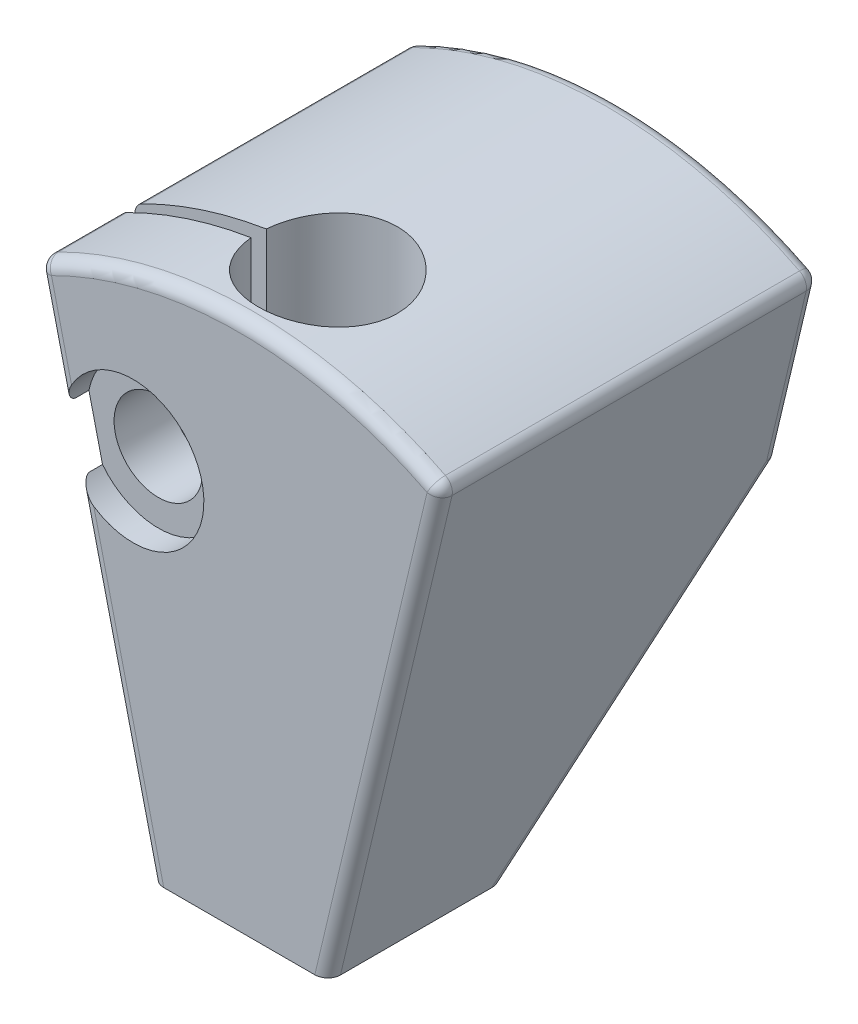
SolidWorks part; units mm, degrees
ref_plane "Plan de face" through (0, 0, 0) normal (0, 0, 1) x (1, 0, 0)
ref_plane "Plan de dessus" through (0, 0, 0) normal (0, 1, 0) x (1, 0, 0)
ref_plane "Plan de droite" through (0, 0, 0) normal (1, 0, 0) x (0, 0, -1)
sketch "Esquisse1" plane through (0, 0, 0) normal (1, 0, 0) x (0, 0, -1)
  line L0 (0, 33.3179) -> (0, -35.6026) construction
  line L1 (3.5, 0) -> (-3.5, 0)
  line L2 (-3.5, 0) -> (-3.5, 21)
  line L3 (-3.5, 21) -> (11.5, 21)
  line L4 (11.5, 21) -> (11.5, 12)
  line L5 (11.5, 12) -> (3.5, 0)
  dimension "D1" = 21
  dimension "D2" = 3.5
  dimension "D3" = 11.5
  dimension "D4" = 12
extrude "Extrusion1" add sketch "Esquisse1" along normal mid plane 16
sketch "Esquisse2" plane through (0, 0, 0) normal (0, 0, 1) x (1, 0, 0)
  line L0 (0, 0) -> (0, 21.9609) construction
  line L1 (-3.5, 0) -> (-8, 19)
  line L2 (8, 0) -> (-8, 0) construction
  line L3 (8, 21) -> (-8, 21) construction
  line L4 (-8, 21) -> (-8, 0) construction
  line L5 (3.5, 0) -> (8, 19)
  line L6 (-3.5, 0) -> (3.5, 0)
  arc A0 (8, 19) -> (-8, 19) centre (0, 4) ccw
  dimension "D1" = 2
  dimension "D2" = 7
extrude "Enlèv. mat.-Extru.1" cut sketch "Esquisse2" against normal through all and the other way through all flip side to cut
fillet "Congé1" radius 0.5 11 edges at (0, 12, -11.5) (5.75, 9.5, 3.5) (7.1711, 15.5, -11.5) (-7.1711, 15.5, -11.5) (0, 21, -11.5) (-8, 19, -4) (-5.75, 9.5, 3.5) (8, 19, -4) (0, 21, 3.5) (-4.9211, 6, -7.5) (4.9211, 6, -7.5)
sketch "Esquisse3" plane through (0, 0, 0) normal (0, 1, 0) x (1, 0, 0)
  circle A0 centre (0, 0) radius 2.75
  dimension "D1" = 5.5
extrude "Enlèv. mat.-Extru.3" cut sketch "Esquisse3" along normal through all
sketch "Esquisse4" plane through (0, 0, 0) normal (0, 1, 0) x (1, 0, 0)
  line L0 (0, 0) -> (-9.5091, 0) construction
  line L1 (-7.9236, 11) -> (-7.9236, -3) construction
  line L2 (-7.9236, 0.3) -> (0, 0.3)
  line L3 (-7.9236, 0.3) -> (-7.9236, -0.3)
  line L4 (-7.9236, -0.3) -> (0, -0.3)
  line L5 (0, 0.3) -> (0, -0.3)
  dimension "D1" = 0.6
extrude "Enlèv. mat.-Extru.4" cut sketch "Esquisse4" along normal through all
sketch "Esquisse5" plane through (0, 0, 3.5) normal (0, 0, 1) x (1, 0, 0)
  circle A0 centre (-4.2, 14) radius 1.25
  dimension "D1" = 2.5
  dimension "D2" = 14
  dimension "D3" = 4.2
extrude "Enlèv. mat.-Extru.5" cut sketch "Esquisse5" against normal blind 14
sketch "Esquisse7" plane through (0, 0, 3.5) normal (0, 0, 1) x (1, 0, 0)
  circle A0 centre (-4.2, 14) radius 1.75
  circle A1 centre (-4.2, 14) radius 1.25 construction
  dimension "D1" = 3.5
extrude "Enlèv. mat.-Extru.7" cut sketch "Esquisse7" against normal up to next
sketch "Esquisse6" plane through (0, 0, 3.5) normal (0, 0, 1) x (1, 0, 0)
  circle A0 centre (-4.2, 14) radius 2.8
  circle A1 centre (-4.2, 14) radius 1.25 construction
  dimension "D1" = 5.6
extrude "Enlèv. mat.-Extru.6" cut sketch "Esquisse6" against normal blind 1
